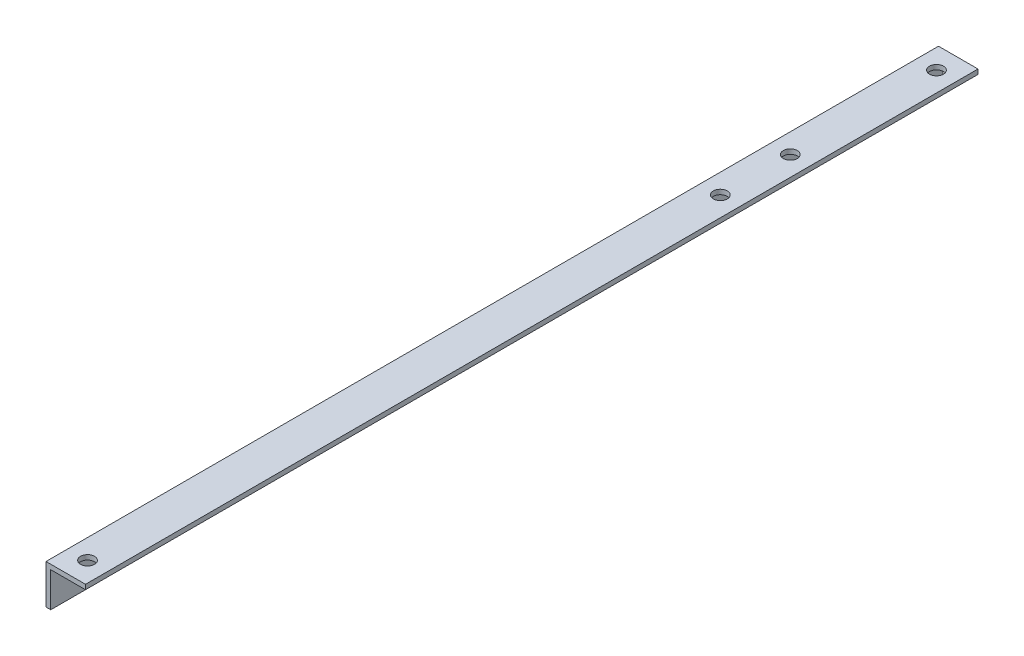
SolidWorks part; units mm, degrees
ref_plane "Front Plane" through (0, 0, 0) normal (0, 0, 1) x (1, 0, 0)
ref_plane "Top Plane" through (0, 0, 0) normal (0, 1, 0) x (1, 0, 0)
ref_plane "Right Plane" through (0, 0, 0) normal (1, 0, 0) x (0, 0, -1)
sketch "Sketch1" plane through (0, 0, 0) normal (0, 0, 1) x (1, 0, 0)
  line L0 (0, 0) -> (12.7, 0)
  line L1 (12.7, 0) -> (12.7, -1.524)
  line L2 (12.7, -1.524) -> (1.524, -1.524)
  line L3 (1.524, -1.524) -> (1.524, -12.7)
  line L4 (1.524, -12.7) -> (0, -12.7)
  line L5 (0, -12.7) -> (0, 0)
  dimension "D1" = 12.7
  dimension "D2" = 1.524
extrude "Boss-Extrude1" add sketch "Sketch1" along normal blind 287
hole_wizard "M4 Clearance Hole1" positions "Sketch2" profile "Sketch3" hole size "M4" standard "ANSI Metric" end condition through all
sketch "Sketch2" plane through (0, 0, 0) normal (0, 1, 0) x (1, 0, 0)
  line L0 (6.35, -7) -> (6.35, 0) construction
  line L1 (12.7, 0) -> (0, 0) construction
  point P0 (6.35, -7)
  point P2 (6.35, -280)
  point P11 (6.35, -54)
  point P13 (6.35, -76.5)
  point P16 (0, 0)
  dimension "D1" = 273
  dimension "D2" = 7
  dimension "D3" = 47
  dimension "D4" = 22.5
sketch "Sketch3" plane through (6.35, 0, 7) normal (1, 0, 0) x (0, 0, 1)
  line L0 (0, 0) -> (0, 12.7)
  line L1 (0, 12.7) -> (2.25, 12.7)
  line L2 (2.25, 12.7) -> (2.25, 0)
  line L5 (2.25, 0) -> (0, 0)
  line L11 (0, -6.35) -> (0, 107.95) construction
  dimension "Thru Hole Dia." = 4.5
  dimension "Thru Hole Depth" = 12.7
hole_wizard "M4 Clearance Hole2" positions "Sketch4" profile "Sketch5" hole size "M4" standard "ANSI Metric" end condition through all
sketch "Sketch4" plane through (0, 0, 0) normal (-1, 0, 0) x (0, 0, 1)
  line L0 (287, 0) -> (0, 0) construction
  line L1 (0, 0) -> (0, -12.7) construction
  point P0 (125, -6.35)
  point P8 (65, -6.35)
  point P10 (185, -6.35)
  point P13 (0, 0)
  dimension "D1" = 6.35
  dimension "D2" = 125
  dimension "D3" = 60
  dimension "D4" = 60
sketch "Sketch5" plane through (0, -6.35, 125) normal (0, 1, 0) x (0, 0, 1)
  line L0 (0, 0) -> (0, 12.7)
  line L1 (0, 12.7) -> (2.25, 12.7)
  line L2 (2.25, 12.7) -> (2.25, 0)
  line L5 (2.25, 0) -> (0, 0)
  line L11 (0, -6.35) -> (0, 107.95) construction
  dimension "Thru Hole Dia." = 4.5
  dimension "Thru Hole Depth" = 12.7
